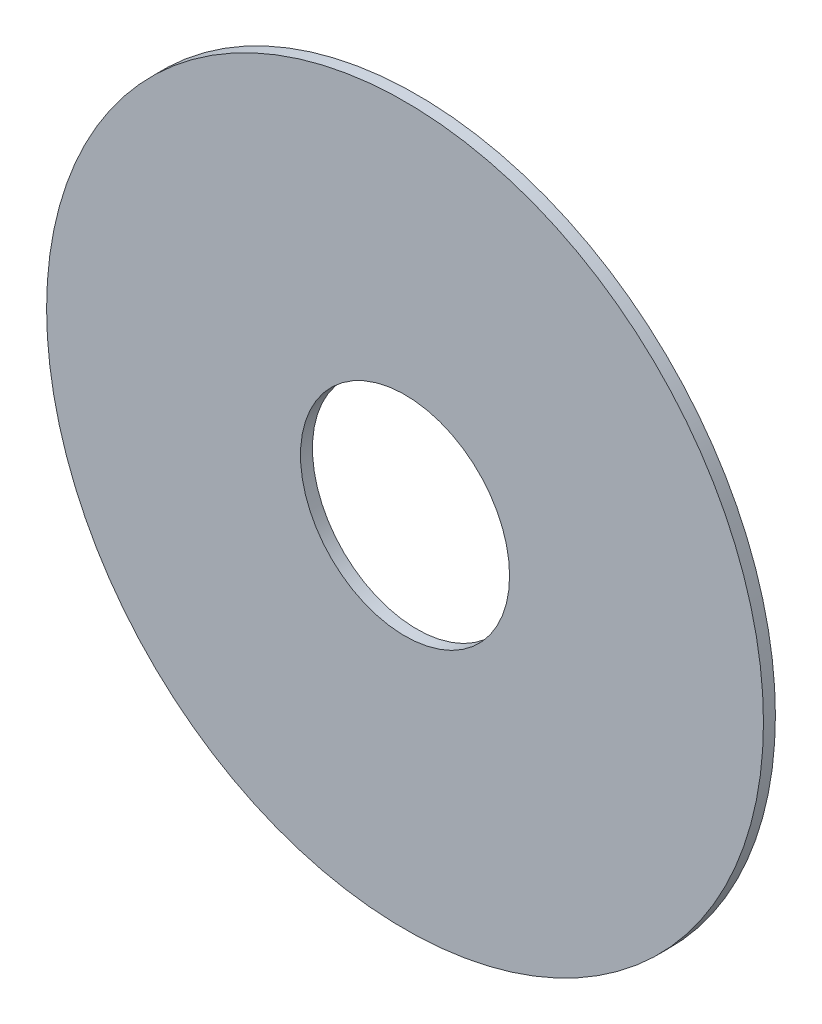
SolidWorks part; units mm, degrees
ref_plane "Front Plane" through (0, 0, 0) normal (0, 0, 1) x (1, 0, 0)
ref_plane "Top Plane" through (0, 0, 0) normal (0, 1, 0) x (1, 0, 0)
ref_plane "Right Plane" through (0, 0, 0) normal (1, 0, 0) x (0, 0, -1)
sketch "Sketch1" plane through (0, 0, 0) normal (0, 0, 1) x (1, 0, 0)
  circle A0 centre (0, 0) radius 15.24
  dimension "D1" = 30.48
extrude "Boss-Extrude1" add sketch "Sketch1" along normal blind 0.508
sketch "Sketch2" plane through (0, 0, 0.508) normal (0, 0, 1) x (1, 0, 0)
  circle A0 centre (0, 0) radius 4.445
  dimension "D1" = 8.89
extrude "Cut-Extrude1" cut sketch "Sketch2" against normal through all
